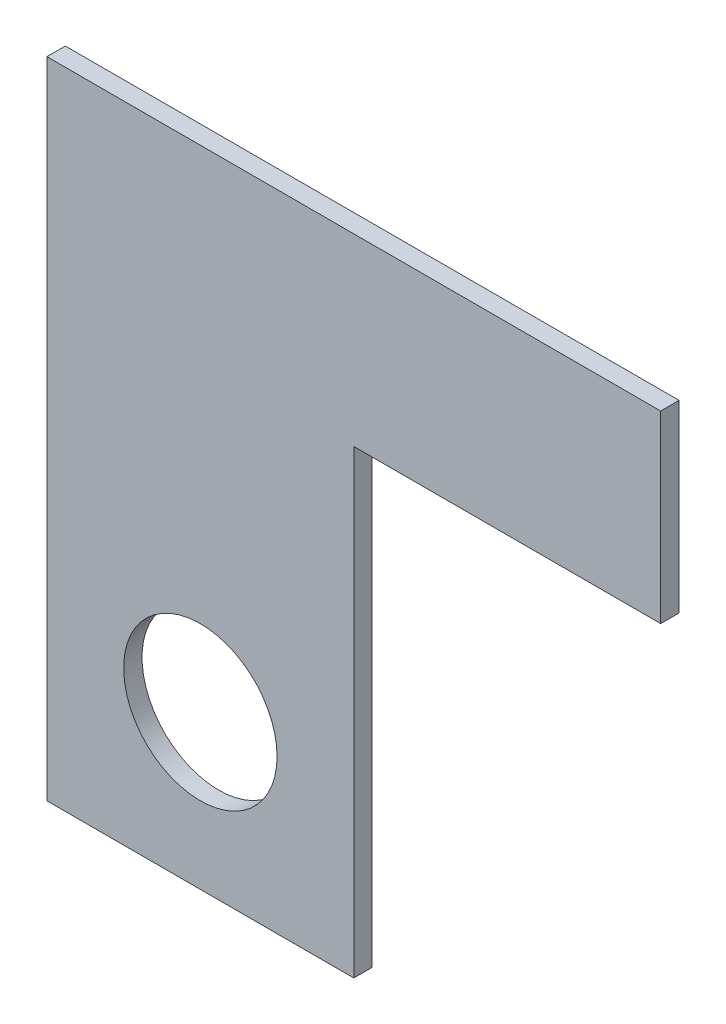
SolidWorks part; units mm, degrees
material "Stainless Steel (ferritic)"
ref_plane "Front Plane" through (0, 0, 0) normal (0, 0, 1) x (1, 0, 0)
ref_plane "Top Plane" through (0, 0, 0) normal (0, 1, 0) x (1, 0, 0)
ref_plane "Right Plane" through (0, 0, 0) normal (1, 0, 0) x (0, 0, -1)
sketch "Sketch1" plane through (0, 0, 0) normal (0, 0, 1) x (1, 0, 0)
  line L1 (-50, -15) -> (50, -15)
  line L2 (-50, -15) -> (-50, 15)
  line L3 (-50, 15) -> (50, 15)
  line L4 (50, -15) -> (50, 15)
  line L5 (-50, -15) -> (50, 15) construction
  line L6 (-50, 15) -> (50, -15) construction
  line L7 (-50, -15) -> (0, -15)
  line L8 (-50, -15) -> (-50, -90)
  line L9 (-50, -90) -> (0, -90)
  line L10 (0, -15) -> (0, -90)
  circle A0 centre (-25, -65) radius 12.5
  point P0 (0, 0)
  dimension "D5" = 25
  dimension "D7" = 25
  dimension "D1" = 100
  dimension "D2" = 30
  dimension "D3" = 75
  dimension "D4" = 50
  dimension "D6" = 25
extrude "Boss-Extrude1" add sketch "Sketch1" along normal blind 3 contours L10 L1 L8 L9 | L1 L4 L3 L2
